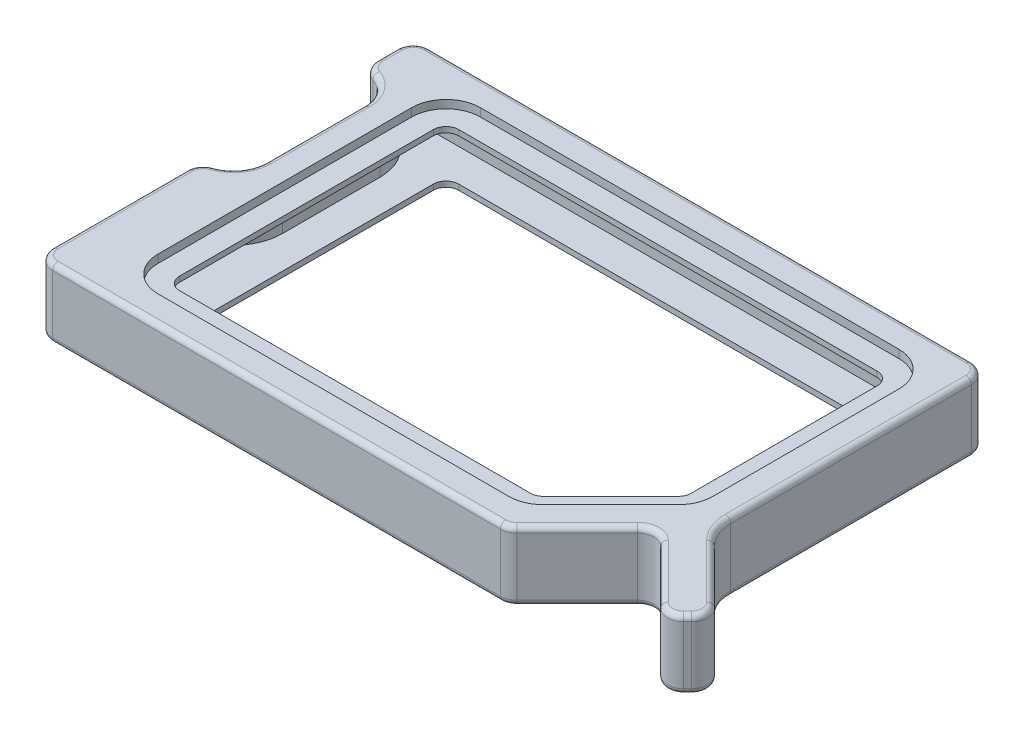
SolidWorks part; units mm, degrees
ref_plane "Front Plane" through (0, 0, 0) normal (0, 0, 1) x (1, 0, 0)
ref_plane "Top Plane" through (0, 0, 0) normal (0, 1, 0) x (1, 0, 0)
ref_plane "Right Plane" through (0, 0, 0) normal (1, 0, 0) x (0, 0, -1)
sketch "Sketch1" plane through (0, 0, 0) normal (0, 1, 0) x (1, 0, 0)
  line L1 (60, 34.7172) -> (-60, 34.7172)
  line L2 (60, 34.7172) -> (60, -34.7172)
  line L3 (60, -34.7172) -> (-60, -34.7172)
  line L4 (-60, 34.7172) -> (-60, -34.7172)
  line L5 (60, 34.7172) -> (-60, -34.7172) construction
  line L6 (60, -34.7172) -> (-60, 34.7172) construction
  point P0 (0, 0)
extrude "Boss-Extrude1" add sketch "Sketch1" along normal blind 6.35
sketch "Sketch2" plane through (0, 6.35, 0) normal (0, 1, 0) x (1, 0, 0)
  line L0 (-60, 19.556) -> (-60, 1.562) construction
  line L1 (-60, 34.7172) -> (-60, -34.7172) construction
  line L2 (-53.9456, 19.556) -> (-53.9456, 1.562)
  line L3 (-66.0544, 19.556) -> (-66.0544, 1.562)
  line L4 (26.766, -34.7172) -> (40.9081, -20.5751)
  line L5 (-60, -34.7172) -> (60, -34.7172) construction
  line L6 (40.9081, -20.5751) -> (55.0503, -34.7172)
  line L7 (55.0503, -34.7172) -> (60, -29.7674)
  line L8 (60, -34.7172) -> (60, 34.7172) construction
  line L9 (60, -29.7674) -> (45.8579, -15.6253)
  line L10 (45.8579, -15.6253) -> (45.8579, 34.7172)
  line L11 (60, 34.7172) -> (-60, 34.7172) construction
  line L12 (40.9081, -20.5751) -> (45.8579, -15.6253) construction
  line L13 (26.766, -34.7172) -> (26.766, -46.9503)
  line L14 (26.766, -46.9503) -> (85.5635, -46.9503)
  line L15 (85.5635, -46.9503) -> (85.5635, 34.7172)
  line L16 (85.5635, 34.7172) -> (45.8579, 34.7172)
  arc A0 (-53.9456, 19.556) -> (-66.0544, 19.556) centre (-60, 19.556) ccw
  arc A1 (-66.0544, 1.562) -> (-53.9456, 1.562) centre (-60, 1.562) ccw
  point P4 (-60, 10.559)
  dimension "D1" = 45
  dimension "D2" = 20
  dimension "D3" = 7
extrude "Cut-Extrude1" cut sketch "Sketch2" against normal through all
fillet "Fillet1" radius 3 9 edges at (40.9081, 3.175, 20.5751) (45.8579, 3.175, -34.7172) (60, 3.175, 29.7674) (55.0503, 3.175, 34.7172) (26.766, 3.175, 34.7172) (-60, 3.175, 34.7172) (-60, 3.175, -34.7172) (-60, 3.175, 4.4924) (-60, 3.175, -25.6104)
sketch "Sketch3" plane through (0, 6.35, 0) normal (0, 1, 0) x (1, 0, 0)
  line L0 (43.0294, -22.6964) -> (47.9792, -17.7466) construction
  line L1 (45.8579, -15.6253) -> (57.8787, -27.6461) construction
  line L2 (45.8579, 31.7172) -> (45.8579, -15.6253) construction
  line L3 (47.9792, -17.7466) -> (49.552, -19.3195)
  line L4 (52.9289, -32.5959) -> (43.0294, -22.6964) construction
  line L5 (49.552, -19.3195) -> (42.6441, -16.5298)
  line L6 (42.6441, -16.5298) -> (45.8579, -12.6234)
  arc A0 (47.9792, -17.7466) -> (45.8579, -12.6234) centre (53.1005, -12.6253) cw
extrude "Boss-Extrude2" add sketch "Sketch3" against normal up to surface (6.35 mm away) up to face at (-3.8667, 0, 5.9096)
sketch "Sketch4" plane through (0, 6.35, 0) normal (0, 1, 0) x (1, 0, 0)
  line L0 (-48.9456, 29.7172) -> (-48.9456, -29.7172)
  line L1 (-48.9456, -29.7172) -> (24.6949, -29.7172)
  line L2 (24.6949, -29.7172) -> (40.8579, -13.5542)
  line L3 (40.8579, -13.5542) -> (40.8579, 29.7172)
  line L4 (40.8579, 29.7172) -> (-48.9456, 29.7172)
  line L6 (38.7868, -22.6964) -> (27.6447, -33.8385) construction
  line L7 (42.8579, 34.7172) -> (-57, 34.7172) construction
  line L10 (-53.9456, 7.3848) -> (-48.9456, 7.3848) construction
  line L11 (-53.9456, 1.562) -> (-53.9456, 19.556) construction
  line L12 (-39.5152, 29.7172) -> (-39.5152, 34.7172) construction
  line L13 (-36.8139, -29.7172) -> (-36.8139, -34.7172) construction
  line L14 (-57, -34.7172) -> (25.5233, -34.7172) construction
  line L15 (30.224, -24.1881) -> (33.7596, -27.7236) construction
  line L16 (40.8579, 14.2223) -> (45.8579, 14.2223) construction
  line L17 (45.8579, 31.7172) -> (45.8579, -12.6253) construction
  dimension "D1" = 5
extrude "Cut-Extrude2" cut sketch "Sketch4" against normal blind 1.5
fillet "Fillet2" radius 6.35 5 edges at (-48.9456, 5.6, 29.7172) (24.6949, 5.6, 29.7172) (40.8579, 5.6, 13.5542) (40.8579, 5.6, -29.7172) (-48.9456, 5.6, -29.7172)
sketch "Sketch5" plane through (0, 4.85, 0) normal (0, 1, 0) x (1, 0, 0)
  line L10 (-44.9456, 23.3672) -> (-44.9456, -23.3672)
  line L11 (-42.5956, -25.7172) -> (22.0647, -25.7172)
  line L12 (23.7264, -25.0289) -> (36.1696, -12.5857)
  line L13 (36.8579, -10.924) -> (36.8579, 23.3672)
  line L14 (34.5079, 25.7172) -> (-42.5956, 25.7172)
  line L15 (-44.9456, 23.3672) -> (-44.9456, -23.3672)
  line L16 (-42.5956, -25.7172) -> (22.0647, -25.7172)
  line L17 (23.7264, -25.0289) -> (36.1696, -12.5857)
  line L18 (36.8579, -10.924) -> (36.8579, 23.3672)
  line L19 (34.5079, 25.7172) -> (-42.5956, 25.7172)
  arc A10 (-44.9456, -23.3672) -> (-42.5956, -25.7172) centre (-42.5956, -23.3672) ccw
  arc A11 (-44.9456, -23.3672) -> (-42.5956, -25.7172) centre (-42.5956, -23.3672) ccw
  arc A12 (22.0647, -25.7172) -> (23.7264, -25.0289) centre (22.0647, -23.3672) ccw
  arc A13 (22.0647, -25.7172) -> (23.7264, -25.0289) centre (22.0647, -23.3672) ccw
  arc A14 (36.1696, -12.5857) -> (36.8579, -10.924) centre (34.5079, -10.924) ccw
  arc A15 (36.1696, -12.5857) -> (36.8579, -10.924) centre (34.5079, -10.924) ccw
  arc A16 (36.8579, 23.3672) -> (34.5079, 25.7172) centre (34.5079, 23.3672) ccw
  arc A17 (36.8579, 23.3672) -> (34.5079, 25.7172) centre (34.5079, 23.3672) ccw
  arc A18 (-42.5956, 25.7172) -> (-44.9456, 23.3672) centre (-42.5956, 23.3672) ccw
  arc A19 (-42.5956, 25.7172) -> (-44.9456, 23.3672) centre (-42.5956, 23.3672) ccw
  dimension "D1" = 4
extrude "Cut-Extrude3" cut sketch "Sketch5" against normal up to next
sketch "Sketch6" plane through (0, 0, 0) normal (0, -1, 0) x (1, 0, 0)
  line L20 (42.8579, -31.7172) -> (42.8579, 12.6253)
  line L21 (45.8579, 19.8679) -> (55.7574, 29.7674)
  line L22 (55.7574, 29.7674) -> (55.0503, 30.4746)
  line L23 (55.0503, 30.4746) -> (45.1508, 20.5751)
  line L24 (36.6655, 20.5751) -> (25.5233, 31.7172)
  line L25 (25.5233, 31.7172) -> (-57, 31.7172)
  line L26 (-57, 31.7172) -> (-57, 6.9809)
  line L27 (-50.9456, -1.562) -> (-50.9456, -19.556)
  line L28 (-57, -28.099) -> (-57, -31.7172)
  line L29 (-57, -31.7172) -> (42.8579, -31.7172)
  line L30 (42.8579, -31.7172) -> (42.8579, 12.6253)
  line L31 (45.8579, 19.8679) -> (55.7574, 29.7674)
  line L32 (55.7574, 29.7674) -> (55.0503, 30.4746)
  line L33 (55.0503, 30.4746) -> (45.1508, 20.5751)
  line L34 (36.6655, 20.5751) -> (25.5233, 31.7172)
  line L35 (25.5233, 31.7172) -> (-57, 31.7172)
  line L36 (-57, 31.7172) -> (-57, 6.9809)
  line L37 (-50.9456, -1.562) -> (-50.9456, -19.556)
  line L38 (-57, -28.099) -> (-57, -31.7172)
  line L39 (-57, -31.7172) -> (42.8579, -31.7172)
  arc A24 (45.8579, 19.8679) -> (42.8579, 12.6253) centre (53.1005, 12.6253) ccw
  arc A25 (36.6655, 20.5751) -> (45.1508, 20.5751) centre (40.9081, 24.8177) ccw
  arc A26 (-50.9456, -1.562) -> (-57, 6.9809) centre (-60, -1.562) ccw
  arc A27 (-57, -28.099) -> (-50.9456, -19.556) centre (-60, -19.556) ccw
  arc A28 (45.8579, 19.8679) -> (42.8579, 12.6253) centre (53.1005, 12.6253) ccw
  arc A29 (36.6655, 20.5751) -> (45.1508, 20.5751) centre (40.9081, 24.8177) ccw
  arc A30 (-50.9456, -1.562) -> (-57, 6.9809) centre (-60, -1.562) ccw
  arc A31 (-57, -28.099) -> (-50.9456, -19.556) centre (-60, -19.556) ccw
  dimension "D1" = 3
extrude "Cut-Extrude4" cut sketch "Sketch6" against normal offset from surface (3.85 mm away) 1 up to face at (1.4849, 4.85, 2.4918)
sketch "Sketch7" plane through (0, 0, 0) normal (0, -1, 0) x (1, 0, 0)
  line L0 (36.6655, 20.5751) -> (41.6152, 15.6253)
  line L1 (42.8579, 12.6253) -> (42.8579, 8.5147)
  line L2 (42.8579, -31.7172) -> (42.8579, 12.6253) construction
  line L3 (36.6655, 20.5751) -> (25.5233, 31.7172) construction
  line L4 (42.8579, 12.6253) -> (57.3368, 29.0383)
  line L5 (57.3368, 29.0383) -> (54.3161, 31.7031)
  line L6 (54.3161, 31.7031) -> (42.8579, 20.5751)
  line L7 (42.8579, 20.5751) -> (36.6655, 20.5751)
  arc A0 (45.8579, 19.8679) -> (42.8579, 12.6253) centre (53.1005, 12.6253) ccw construction
  arc A1 (42.8579, 12.6253) -> (41.6152, 15.6253) centre (38.6152, 12.6253) ccw
  line M1 (45.1508, 20.5751) -> (55.0503, 30.4746)
  line M2 (55.0503, 30.4746) -> (55.7574, 29.7674)
  line M3 (55.7574, 29.7674) -> (45.8579, 19.8679)
  arc M4 (45.8579, 19.8679) -> (42.8579, 12.6253) centre (53.1005, 12.6253) ccw
  arc M14 (36.6655, 20.5751) -> (45.1508, 20.5751) centre (40.9081, 24.8177) ccw
extrude "Boss-Extrude3" add sketch "Sketch7" against normal up to surface (3.85 mm away) contours A1 L0 M4 M3 M2 M1 M14 up to face at (1.5593, 3.85, 6.4422)
fillet "Fillet4" radius 1 22 edges at (-55.0603, 6.35, 1.9387) (-59.4476, 6.35, 5.2463) (-60, 6.35, 19.3491) (-59.1213, 6.35, 33.8385) (-15.7383, 6.35, 34.7172) (26.6714, 6.35, 34.4888) (33.2157, 6.35, 28.2674) (40.9081, 6.35, 21.8177) (47.9792, 6.35, 27.6461) (55.0503, 6.35, 33.4746) (57.5251, 6.35, 32.2423) (58.7574, 6.35, 29.7674) (52.9289, 6.35, 22.6964) (46.4092, 6.35, 15.3969) (45.8579, 6.35, -9.5459) (44.9792, 6.35, -33.8385) (-7.0711, 6.35, -34.7172) (-59.1213, 6.35, -33.8385) (-60, 6.35, -29.9081) (-59.4476, 6.35, -26.3643) (-55.0603, 6.35, -23.0568) (-53.9456, 6.35, -10.559)
mirror "Mirror1" about plane through (0, 0, 0) normal (0, -1, 0) of bodies 107
sketch "Sketch8" plane through (-60, 0, 0) normal (-1, 0, 0) x (0, 0, 1)
  line L0 (9.8427, 1.7996) -> (18.1786, 1.7996)
  line L1 (18.1786, 1.7996) -> (16.1006, -1.7996)
  line L2 (16.1006, -1.7996) -> (11.9207, -1.7996)
  line L3 (11.9207, -1.7996) -> (9.8427, 1.7996)
  line L4 (-15.556, 0) -> (26.9137, 0) construction
  line L5 (-19.556, -5.35) -> (-19.556, 5.35) construction
  line L6 (-1.562, -5.35) -> (-1.562, 5.35) construction
  circle A0 centre (-15.556, 0) radius 1.7996
  circle A1 centre (-5.562, 0) radius 1.7996
  circle A2 centre (26.9137, 0) radius 1.7996
  circle A3 centre (-15.556, 0) radius 4 construction
  circle A4 centre (-5.562, 0) radius 4 construction
  point P8 (10.8817, 0)
  point P11 (17.1396, 0)
  dimension "D3" = 8
  dimension "D1" = 60
  dimension "D2" = 60
extrude "Cut-Extrude5" cut sketch "Sketch8" against normal blind 21
fillet "Fillet5" radius 1 4 edges at (-58.5, -1.7996, 16.1006) (-58.5, 1.7996, 18.1786) (-58.5, 1.7996, 9.8427) (-58.5, -1.7996, 11.9207)
ref_plane "Plane1" through (12.6414, 0, -12.6414) normal (-0.7071, 0, 0.7071) x (0.7071, 0, 0.7071)
sketch "Sketch9" plane through (12.6414, 0, -12.6414) normal (-0.7071, 0, 0.7071) x (0.7071, 0, 0.7071)
  line L1 (47.1347, -4.8191) -> (59.9349, -4.8191)
  line L2 (47.1347, -4.8191) -> (47.1347, 4.8191)
  line L3 (47.1347, 4.8191) -> (59.9349, 4.8191)
  line L4 (59.9349, -4.8191) -> (59.9349, 4.8191)
  line L5 (47.1347, -4.8191) -> (59.9349, 4.8191) construction
  line L6 (47.1347, 4.8191) -> (59.9349, -4.8191) construction
  point P0 (53.5348, 0)
extrude "Cut-Extrude6" cut sketch "Sketch9" along normal blind 1.6 from surface at -3.5 starting at face at (52.9289, 0, 22.6964)
